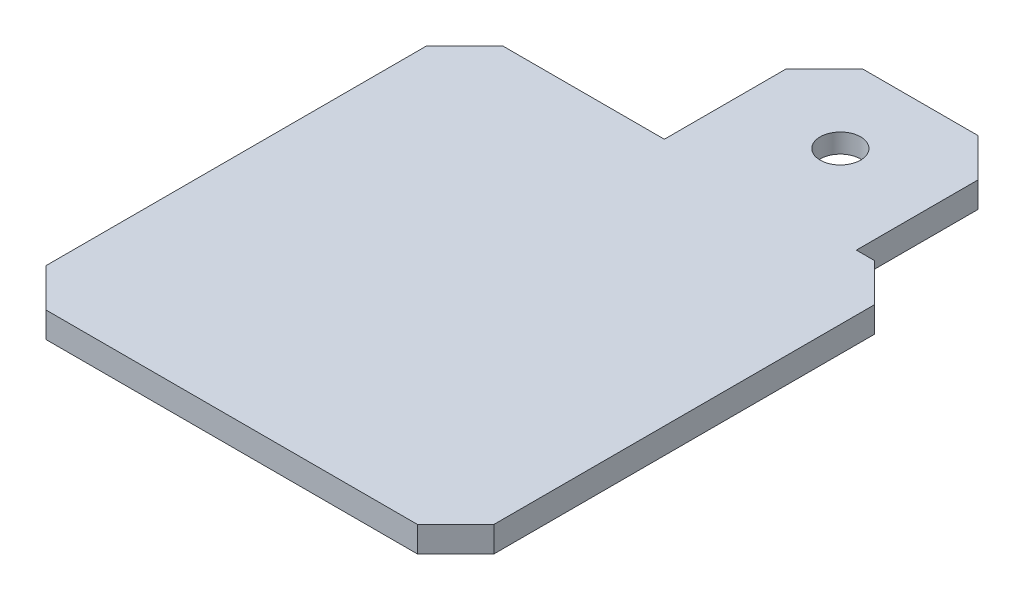
SolidWorks part; units mm, degrees
ref_plane "Front Plane" through (0, 0, 0) normal (0, 0, 1) x (1, 0, 0)
ref_plane "Top Plane" through (0, 0, 0) normal (0, 1, 0) x (1, 0, 0)
ref_plane "Right Plane" through (0, 0, 0) normal (1, 0, 0) x (0, 0, -1)
sketch "Sketch1" plane through (0, 0, 0) normal (0, 1, 0) x (1, 0, 0)
  line L0 (0, 17.5) -> (0, 30) construction
  line L1 (-17.5, -17.5) -> (17.5, -17.5)
  line L2 (-17.5, -17.5) -> (-17.5, 17.5)
  line L3 (-17.5, 17.5) -> (17.5, 17.5)
  line L4 (17.5, -17.5) -> (17.5, 17.5)
  line L5 (-17.5, -17.5) -> (17.5, 17.5) construction
  line L6 (-17.5, 17.5) -> (17.5, -17.5) construction
  line L7 (7.5, 17.5) -> (-7.5, 17.5) construction
  line L8 (-7.5, 17.5) -> (-7.5, 30) construction
  line L9 (7.5, 17.5) -> (7.5, 30)
  line L10 (7.5, 30) -> (-1.9, 30)
  line L11 (7.5, 17.5) -> (13.1, 17.5) construction
  line L12 (13.1, 17.5) -> (13.1, 30)
  line L13 (13.1, 30) -> (7.5, 30)
  line L14 (-7.5, 17.5) -> (-1.9, 17.5) construction
  line L15 (-1.9, 17.5) -> (-1.9, 30)
  line L16 (13.1, 23.75) -> (-1.9, 23.75) construction
  line L17 (-17.5, -17.5) -> (-17.5, -18.2)
  line L18 (-17.5, -18.2) -> (17.5, -18.2)
  line L19 (17.5, -18.2) -> (17.5, -17.5)
  circle A1 centre (0, 23.75) radius 2.5 construction
  circle A2 centre (5.6, 23.75) radius 2.6
  point P0 (0, 0)
  point P11 (0, 17.5)
  dimension "D3" = 5
  dimension "D7" = 5.2
  dimension "D1" = 35
  dimension "D2" = 12.5
  dimension "D4" = 7.5
  dimension "D5" = 5.6
  dimension "D6" = 5.6
  dimension "D8" = 0.7
extrude "Boss-Extrude1" add sketch "Sketch1" along normal blind 2 contours A2 L9 L3 L12 L13 | A2 L9 L10 L15 L3 | L18 L19 L1 L17 | L1 L4 L3 L2
chamfer "Chamfer1" distance 3 angle 45 6 edges at (13.1, 1, -30) (-1.9, 1, -30) (17.5, 1, 18.2) (17.5, 1, -17.5) (-17.5, 1, 18.2) (-17.5, 1, -17.5)
ref_plane "Plane2" through (0, 2, 0) normal (0, 1, 0) x (1, 0, 0)
sketch "Sketch4" plane through (0, 2, 0) normal (0, 1, 0) x (1, 0, 0)
  circle A0 centre (5.6, 23.75) radius 2.6
  circle A1 centre (5.6, 23.75) radius 1.58
  dimension "D1" = 5.2
  dimension "D2" = 3.16
extrude "Boss-Extrude2" add sketch "Sketch4" against normal blind 1.5
